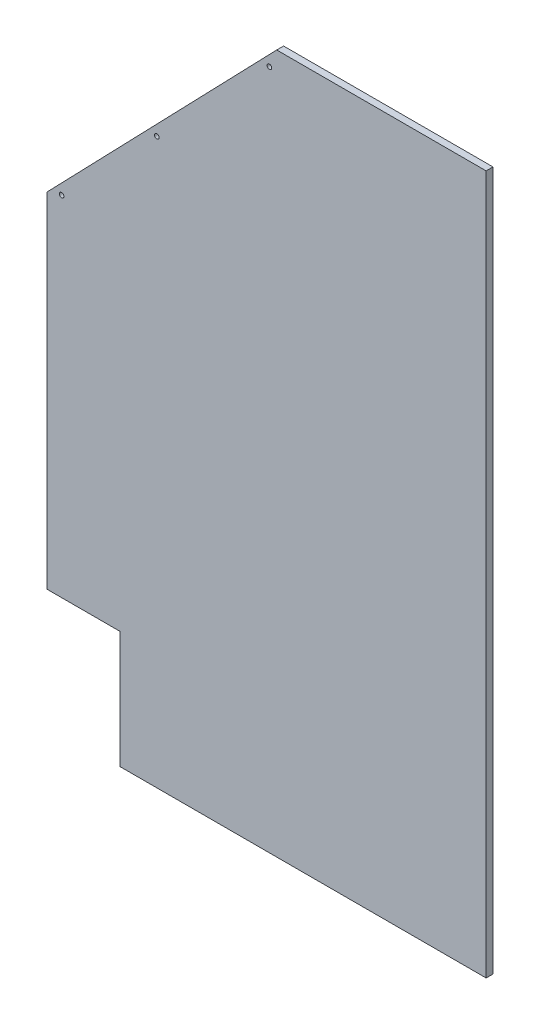
SolidWorks part; units mm, degrees
material "Pine"
ref_plane "Front Plane" through (0, 0, 0) normal (0, 0, 1) x (1, 0, 0)
ref_plane "Top Plane" through (0, 0, 0) normal (0, 1, 0) x (1, 0, 0)
ref_plane "Right Plane" through (0, 0, 0) normal (1, 0, 0) x (0, 0, -1)
sketch "Sketch1" plane through (0, 0, 0) normal (0, 0, 1) x (1, 0, 0)
  line L0 (1068.4674, -524.1043) -> (941.4674, -524.1043)
  line L1 (70.0554, 485.5457) -> (669.8794, 485.5457)
  line L2 (-328.5326, 72.7957) -> (-328.5326, -524.1043)
  line L3 (-201.5326, -727.3043) -> (941.4674, -727.3043)
  line L4 (1068.4674, 72.7957) -> (1068.4674, -524.1043)
  line L5 (-328.5326, -524.1043) -> (-201.5326, -524.1043)
  line L6 (-201.5326, -524.1043) -> (-201.5326, -727.3043)
  line L7 (369.9674, -727.3043) -> (369.9674, -138.7274) construction
  line L8 (-328.5326, -524.1043) -> (-328.5326, 72.7957) construction
  line L9 (-328.5326, 72.7957) -> (70.0554, 485.5457)
  line L10 (941.4674, -524.1043) -> (941.4674, -727.3043)
  line L11 (1068.4674, -524.1043) -> (1068.4674, 72.7957) construction
  line L12 (1068.4674, 72.7957) -> (669.8794, 485.5457)
  line L13 (369.9674, 485.5457) -> (369.9674, -138.7274) construction
  dimension "D2" = 127
  dimension "D3" = 596.9
  dimension "D4" = 127
  dimension "D5" = 596.9
  dimension "D6" = 136
  dimension "D7" = 136
extrude "Boss-Extrude1" add sketch "Sketch1" along normal blind 11.9062
hole_wizard "5/16 (0.3125) Diameter Hole1" positions "Sketch2" profile "Sketch3" hole size "5/16" standard "ANSI Inch" end condition through all
sketch "Sketch2" plane through (0, 0, 11.9062) normal (0, 0, 1) x (1, 0, 0)
  line L0 (70.0554, 485.5457) -> (-328.5326, 72.7957) construction
  line L1 (-328.5326, 72.7957) -> (-328.5326, -524.1043) construction
  line L2 (1068.4674, 72.7957) -> (669.8794, 485.5457) construction
  point P0 (-303.1326, 80.8158)
  point P2 (-138.0326, 251.7819)
  point P4 (57.3554, 454.1121)
  point P6 (682.5794, 454.1121)
  point P8 (877.9674, 251.7819)
  point P10 (1043.0674, 80.8158)
  dimension "D1" = 12.7
  dimension "D2" = 12.7
  dimension "D3" = 12.7
  dimension "D4" = 25.4
  dimension "D5" = 12.7
  dimension "D6" = 12.7
  dimension "D7" = 12.7
  dimension "D8" = 12.7
  dimension "D9" = 190.5
sketch "Sketch3" plane through (-303.1326, 80.8158, 11.9062) normal (1, 0, 0) x (0, -1, 0)
  line L0 (0, 0) -> (0, 11.9062)
  line L1 (0, 11.9062) -> (3.9687, 11.9062)
  line L2 (3.9687, 11.9062) -> (3.9687, 0)
  line L5 (3.9687, 0) -> (0, 0)
  line L11 (0, -6.35) -> (0, 107.95) construction
  dimension "Thru Hole Dia." = 7.9375
  dimension "Thru Hole Depth" = 11.9062
sketch "Sketch4" plane through (0, 0, 11.9062) normal (0, 0, 1) x (1, 0, 0)
  line L0 (669.8794, 485.5457) -> (70.0554, 485.5457) construction
  line L1 (1068.4674, -727.3043) -> (433.4674, -727.3043)
  line L2 (1068.4674, -727.3043) -> (1068.4674, 485.5457)
  line L3 (1068.4674, 485.5457) -> (433.4674, 485.5457)
  line L4 (433.4674, -727.3043) -> (433.4674, 485.5457)
  line L5 (1068.4674, -524.1043) -> (1068.4674, 72.7957) construction
  dimension "D1" = 635
extrude "Cut-Extrude1" cut sketch "Sketch4" against normal through all
